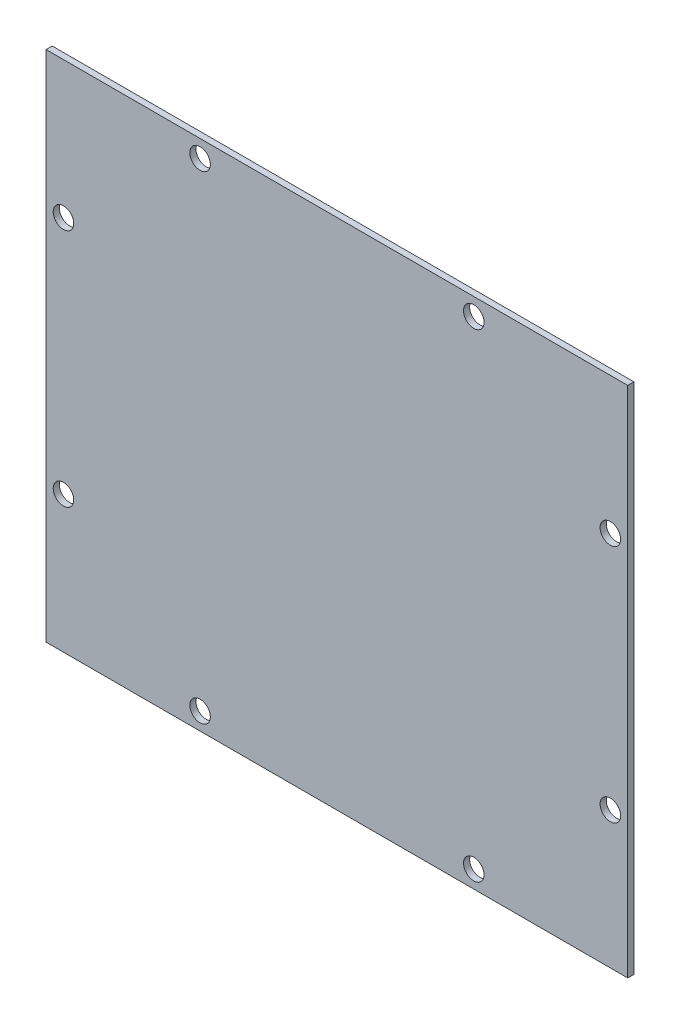
SolidWorks part; units mm, degrees
material "6061 Alloy"
ref_plane "Front Plane" through (0, 0, 0) normal (0, 0, 1) x (1, 0, 0)
ref_plane "Top Plane" through (0, 0, 0) normal (0, 1, 0) x (1, 0, 0)
ref_plane "Right Plane" through (0, 0, 0) normal (1, 0, 0) x (0, 0, -1)
sketch "Sketch1" plane through (0, 0, 0) normal (0, 0, 1) x (1, 0, 0)
  line L1 (-212.5, -187.5) -> (212.5, -187.5)
  line L2 (-212.5, -187.5) -> (-212.5, 187.5)
  line L3 (-212.5, 187.5) -> (212.5, 187.5)
  line L4 (212.5, -187.5) -> (212.5, 187.5)
  line L5 (-212.5, -187.5) -> (212.5, 187.5) construction
  line L6 (-212.5, 187.5) -> (212.5, -187.5) construction
  point P0 (0, 0)
  dimension "D1" = 425
  dimension "D2" = 375
extrude "Boss-Extrude1" add sketch "Sketch1" against normal blind 4.5
sketch "Sketch2" plane through (0, 0, 0) normal (0, 0, 1) x (1, 0, 0)
  line L5 (0, 174.8) -> (-212.5, 174.8) construction
  line L10 (-212.5, 187.5) -> (-212.5, -187.5) construction
  line L13 (0, 56.2076) -> (0, -72.6903) construction
  line L14 (-85.888, 0) -> (100.7916, 0) construction
  line L15 (-199.8, 0) -> (-199.8, 187.5) construction
  line L16 (212.5, 187.5) -> (-212.5, 187.5) construction
  circle A10 centre (-199.8, 87.5) radius 7.5
  circle A11 centre (-100, 174.8) radius 7.5
  circle A12 centre (100, 174.8) radius 7.5
  circle A13 centre (199.8, 87.5) radius 7.5
  circle A14 centre (-100, -174.8) radius 7.5
  circle A15 centre (-199.8, -87.5) radius 7.5
  circle A16 centre (199.8, -87.5) radius 7.5
  circle A17 centre (100, -174.8) radius 7.5
  dimension "D3" = 15
  dimension "D1" = 12.7
  dimension "D2" = 12.7
  dimension "D4" = 200
  dimension "D5" = 175
extrude "Cut-Extrude1" cut sketch "Sketch2" against normal through all both and the other way through all
equation "\"Critical Fastener Diameter\"= 10mm"
equation "\"Insert Wall Thickness\"= 5mm"
equation "\"D3@Sketch2\" = \"Critical Fastener Diameter\" + \"Insert Wall Thickness\""
